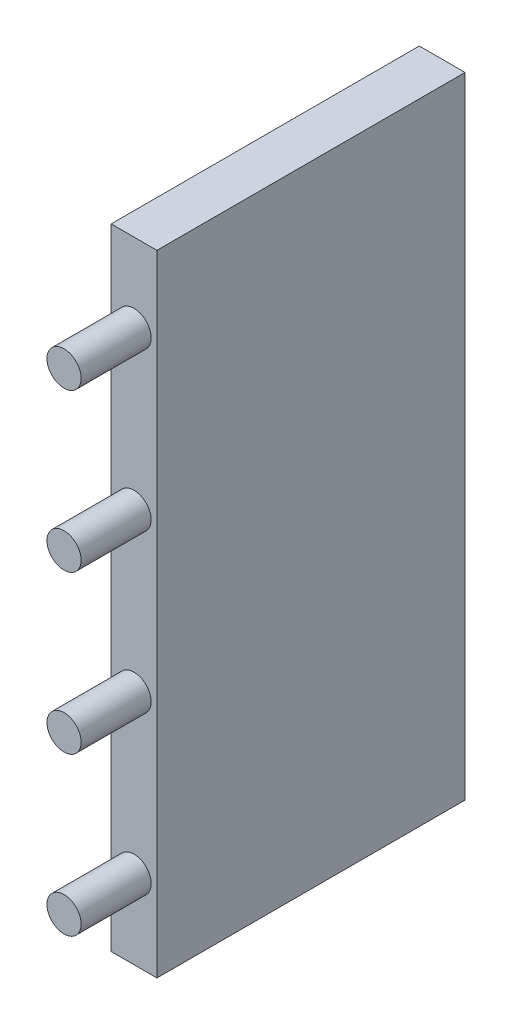
SolidWorks part; units mm, degrees
ref_plane "Front Plane" through (0, 0, 0) normal (0, 0, 1) x (1, 0, 0)
ref_plane "Top Plane" through (0, 0, 0) normal (0, 1, 0) x (1, 0, 0)
ref_plane "Right Plane" through (0, 0, 0) normal (1, 0, 0) x (0, 0, -1)
sketch "Sketch1" plane through (0, 0, 0) normal (1, 0, 0) x (0, 0, -1)
  line L0 (-27.94, 57.15) -> (27.94, -57.15) construction
  line L1 (-27.94, 57.15) -> (27.94, 57.15)
  line L2 (-27.94, 57.15) -> (-27.94, -57.15)
  line L3 (-27.94, -57.15) -> (27.94, -57.15)
  line L4 (27.94, 57.15) -> (27.94, -57.15)
  point P4 (0, 0)
  dimension "D1" = 55.88
  dimension "D2" = 114.3
extrude "Boss-Extrude1" add sketch "Sketch1" along normal blind 8.3
sketch "Sketch2" plane through (0, 0, 27.94) normal (0, 0, 1) x (1, 0, 0)
  line L0 (4.15, -57.15) -> (4.15, -61.5) construction
  line L1 (8.3, -57.15) -> (0, -57.15) construction
  circle A0 centre (4.15, -42.8625) radius 3.1
  dimension "D1" = 6.2
  dimension "D2" = 14.2875
extrude "Boss-Extrude2" add sketch "Sketch2" along normal blind 12.7
pattern_linear "LPattern1" count 4 spacing 28.575 along (0, 1, 0) of "Boss-Extrude2"
